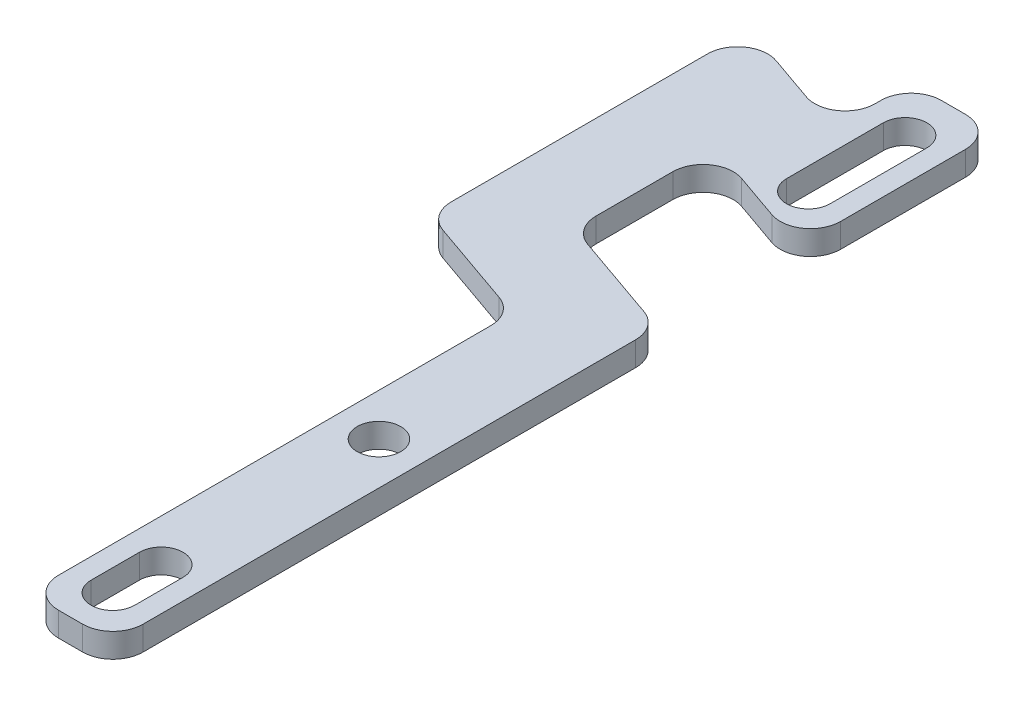
SolidWorks part; units mm, degrees
ref_plane "Спереди" through (0, 0, 0) normal (0, 0, 1) x (1, 0, 0)
ref_plane "Сверху" through (0, 0, 0) normal (0, 1, 0) x (1, 0, 0)
ref_plane "Справа" through (0, 0, 0) normal (1, 0, 0) x (0, 0, -1)
sketch "Эскиз1" plane through (0, 165.3226, 0) normal (0, -1, 0) x (1, 0, 0)
  line L0 (-228.0213, -139.1955) -> (-228.0213, -155.1955)
  line L1 (-220.8213, -139.1955) -> (-220.8213, -155.1955)
  line L2 (-228.0213, -24.1955) -> (-228.0213, -32.1955)
  line L3 (-220.8213, -24.1955) -> (-220.8213, -32.1955)
  line L4 (-231.4213, -112.0832) -> (-235.0694, -113.3568)
  line L5 (-226.4213, -17.1955) -> (-222.4213, -17.1955)
  line L6 (-231.4213, -22.1955) -> (-231.4213, -93.7041)
  line L7 (-226.4213, -163.1955) -> (-222.4213, -163.1955)
  line L8 (-217.4213, -22.1955) -> (-217.4213, -103.6451)
  line L9 (-238.4213, -118.0773) -> (-238.4213, -130.7876)
  line L10 (-231.7733, -135.5082) -> (-231.4213, -135.3853)
  line L11 (-234.7733, -98.4247) -> (-249.0694, -103.4158)
  line L12 (-252.4213, -108.1363) -> (-252.4213, -150.504)
  line L13 (-245.7733, -155.2245) -> (-238.0694, -152.535)
  line L16 (-231.4213, -112.0832) -> (-220.7733, -108.3657)
  line L17 (-231.4213, -135.3853) -> (-224.0694, -132.8186)
  line L18 (-217.4213, -137.5392) -> (-217.4213, -158.1955)
  line L19 (-231.4213, -157.2555) -> (-231.4213, -158.1955)
  arc A0 (-220.8213, -24.1955) -> (-228.0213, -24.1955) centre (-224.4213, -24.1955) ccw
  arc A1 (-228.0213, -32.1955) -> (-220.8213, -32.1955) centre (-224.4213, -32.1955) ccw
  circle A2 centre (-224.4213, -68.1955) radius 3.6
  arc A3 (-226.4213, -163.1955) -> (-231.4213, -158.1955) centre (-226.4213, -158.1955) cw
  arc A4 (-222.4213, -163.1955) -> (-217.4213, -158.1955) centre (-222.4213, -158.1955) ccw
  arc A5 (-222.4213, -17.1955) -> (-217.4213, -22.1955) centre (-222.4213, -22.1955) cw
  arc A6 (-226.4213, -17.1955) -> (-231.4213, -22.1955) centre (-226.4213, -22.1955) ccw
  arc A7 (-228.0213, -155.1955) -> (-220.8213, -155.1955) centre (-224.4213, -155.1955) ccw
  arc A8 (-220.8213, -139.1955) -> (-228.0213, -139.1955) centre (-224.4213, -139.1955) ccw
  arc A9 (-231.4213, -93.7041) -> (-234.7733, -98.4247) centre (-236.4213, -93.7041) cw
  arc A10 (-245.7733, -155.2245) -> (-252.4213, -150.504) centre (-247.4213, -150.504) cw
  arc A11 (-231.7733, -135.5082) -> (-238.4213, -130.7876) centre (-233.4213, -130.7876) cw
  arc A12 (-235.0694, -113.3568) -> (-238.4213, -118.0773) centre (-233.4213, -118.0773) ccw
  arc A13 (-249.0694, -103.4158) -> (-252.4213, -108.1363) centre (-247.4213, -108.1363) ccw
  arc A14 (-231.4213, -157.2555) -> (-238.0694, -152.535) centre (-236.4213, -157.2555) ccw
  arc A15 (-217.4213, -103.6451) -> (-220.7733, -108.3657) centre (-222.4213, -103.6451) cw
  arc A16 (-217.4213, -137.5392) -> (-224.0694, -132.8186) centre (-222.4213, -137.5392) ccw
  point P4 (-224.4213, -68.1955)
  point P10 (-224.4213, -29.1955)
  point P51 (-231.4213, -150.214)
  point P54 (-217.4213, -107.1955)
  point P57 (-217.4213, -130.4977)
  dimension "D3" = 7.2
  dimension "D4" = 7.2
  dimension "D5" = 7.2
  dimension "D14" = 5
  dimension "D6" = 7.2
  dimension "D9" = 7
  dimension "D16" = 87
  dimension "D17" = 7.2
  dimension "D18" = 16
  dimension "D27" = 5
  dimension "D28" = 5
  dimension "D2" = 5
  dimension "D7" = 39
  dimension "D8" = 3
  dimension "D10" = 7
  dimension "D11" = 7
  dimension "D12" = 7
  dimension "D13" = 95
  dimension "D15" = 7
  dimension "D19" = 14
  dimension "D20" = 39
  dimension "D21" = 14
  dimension "D22" = 14
  dimension "D23" = 7
  dimension "D24" = 14
  dimension "D25" = 22
  dimension "D26" = 109.245
extrude "Бобышка-Вытянуть1" add sketch "Эскиз1" along normal blind 4
